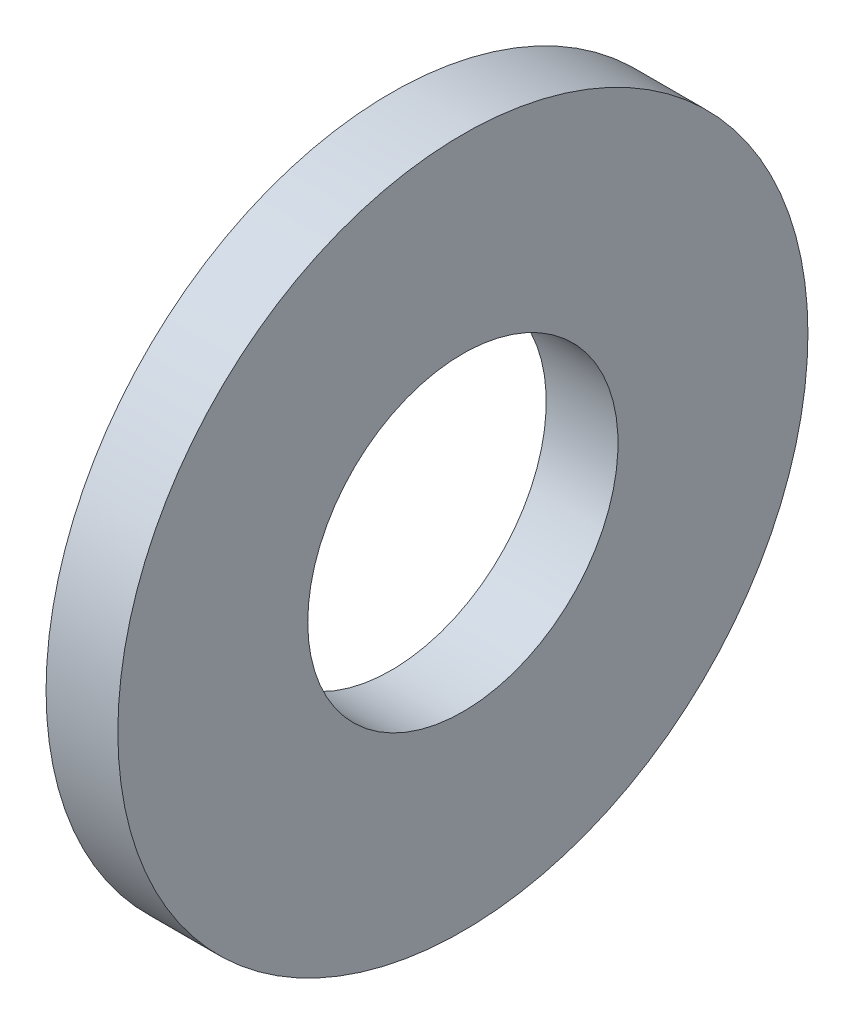
SolidWorks part; units mm, degrees
ref_plane "Plane1" through (0, 0, 0) normal (0, 0, 1) x (1, 0, 0)
ref_plane "Plane2" through (0, 0, 0) normal (0, 1, 0) x (1, 0, 0)
ref_plane "Plane3" through (0, 0, 0) normal (1, 0, 0) x (0, 0, -1)
sketch "Sketch1" plane through (0, 0, 0) normal (0, 0, 1) x (1, 0, 0)
  line L0 (-34.925, 0) -> (9.525, 0) construction
  line L1 (0, 3.5687) -> (0, 7.9375)
  line L2 (0, 7.9375) -> (-1.651, 7.9375)
  line L3 (-1.651, 7.9375) -> (-1.651, 3.5687)
  line L4 (-1.651, 3.5687) -> (0, 3.5687)
  dimension "Thickness" = 1.651
  dimension "Inside_dia" = 7.1374
  dimension "Outside_dia" = 15.875
revolve "Base-Revolve" add sketch "Sketch1" angle 360 about L0
